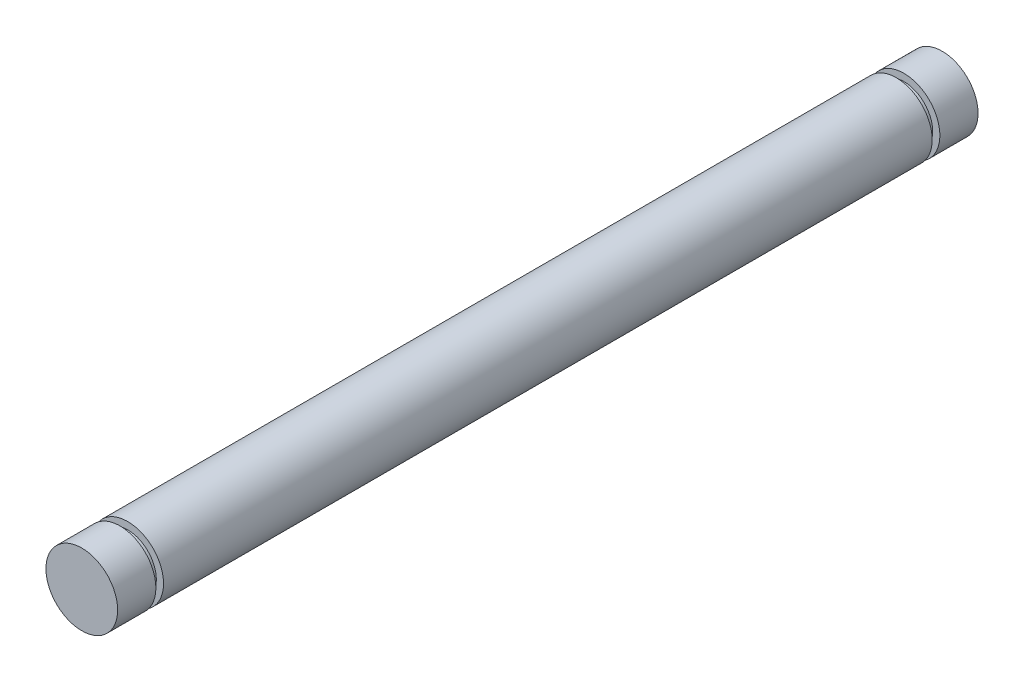
SolidWorks part; units mm, degrees
ref_plane "Front Plane" through (0, 0, 0) normal (0, 0, 1) x (1, 0, 0)
ref_plane "Top Plane" through (0, 0, 0) normal (0, 1, 0) x (1, 0, 0)
ref_plane "Right Plane" through (0, 0, 0) normal (1, 0, 0) x (0, 0, -1)
sketch "Sketch1" plane through (0, 0, 0) normal (0, 0, 1) x (1, 0, 0)
  circle A0 centre (0, 0) radius 4.7625
  dimension "D1" = 9.525
extrude "Boss-Extrude1" add sketch "Sketch1" along normal blind 102.108
sketch "Sketch2" plane through (0, 0, 0) normal (0, 0, -1) x (-1, 0, 0)
  circle A0 centre (0, 0) radius 3.81
  dimension "D1" = 7.62
extrude "Boss-Extrude2" add sketch "Sketch2" along normal blind 1.016
sketch "Sketch3" plane through (0, 0, -1.016) normal (0, 0, -1) x (-1, 0, 0)
  circle A0 centre (0, 0) radius 4.7625
  dimension "D1" = 9.525
extrude "Boss-Extrude3" add sketch "Sketch3" along normal blind 5.08
sketch "Sketch4" plane through (0, 0, 102.108) normal (0, 0, 1) x (1, 0, 0)
  circle A0 centre (0, 0) radius 3.81
  dimension "D1" = 7.62
extrude "Boss-Extrude4" add sketch "Sketch4" along normal blind 1.016
sketch "Sketch5" plane through (0, 0, 103.124) normal (0, 0, 1) x (1, 0, 0)
  circle A0 centre (0, 0) radius 4.7625
  dimension "D1" = 9.525
extrude "Boss-Extrude5" add sketch "Sketch5" along normal blind 5.08
